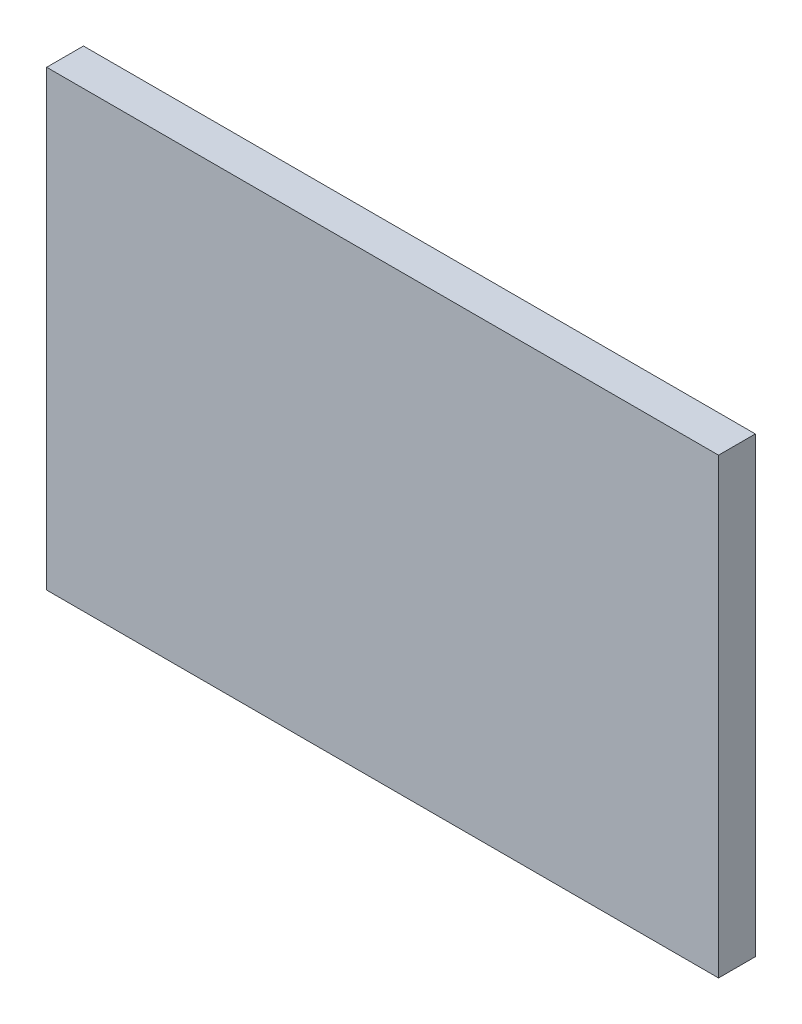
SolidWorks part; units mm, degrees
ref_plane "Front Plane" through (0, 0, 0) normal (0, 0, 1) x (1, 0, 0)
ref_plane "Top Plane" through (0, 0, 0) normal (0, 1, 0) x (1, 0, 0)
ref_plane "Right Plane" through (0, 0, 0) normal (1, 0, 0) x (0, 0, -1)
sketch "Sketch1" plane through (0, 0, 0) normal (0, 0, 1) x (1, 0, 0)
  line L1 (14.605, -9.8425) -> (-14.605, -9.8425)
  line L2 (14.605, -9.8425) -> (14.605, 9.8425)
  line L3 (14.605, 9.8425) -> (-14.605, 9.8425)
  line L4 (-14.605, -9.8425) -> (-14.605, 9.8425)
  line L5 (14.605, -9.8425) -> (-14.605, 9.8425) construction
  line L6 (14.605, 9.8425) -> (-14.605, -9.8425) construction
  point P0 (0, 0)
  dimension "D1" = 19.685
  dimension "D2" = 29.21
extrude "Boss-Extrude1" add sketch "Sketch1" along normal blind 1.6
